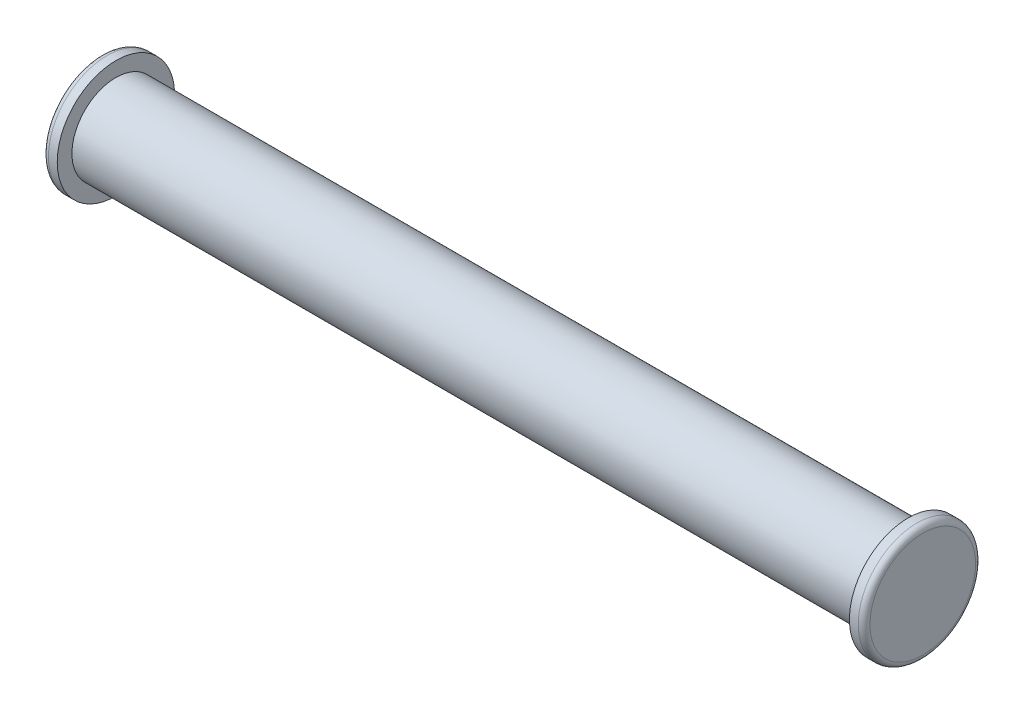
SolidWorks part; units mm, degrees
material "AISI 304"
ref_plane "Front" through (0, 0, 0) normal (0, 0, 1) x (1, 0, 0)
ref_plane "Top" through (0, 0, 0) normal (0, 1, 0) x (1, 0, 0)
ref_plane "Right" through (0, 0, 0) normal (1, 0, 0) x (0, 0, -1)
sketch "Sketch1" plane through (0, 0, 0) normal (1, 0, 0) x (0, 0, -1)
  circle A0 centre (0, 0) radius 1.5
  dimension "D1" = 3
extrude "Boss-Extrude1" add sketch "Sketch1" along normal mid plane 27
sketch "Sketch2" plane through (13.5, 0, 0) normal (1, 0, 0) x (0, 0, -1)
  circle A0 centre (0, 0) radius 2
  dimension "D1" = 4
extrude "Boss-Extrude2" add sketch "Sketch2" along normal blind 0.5
sketch "Sketch3" plane through (-13.5, 0, 0) normal (-1, 0, 0) x (0, 0, 1)
  circle A1 centre (0, 0) radius 2
  circle A2 centre (0, 0) radius 2
  dimension "D1" = 0
extrude "Boss-Extrude3" add sketch "Sketch3" along normal blind 0.5
fillet "Fillet1" radius 0.2 2 edges at (14, 0, -2) (-14, 0, 2)
